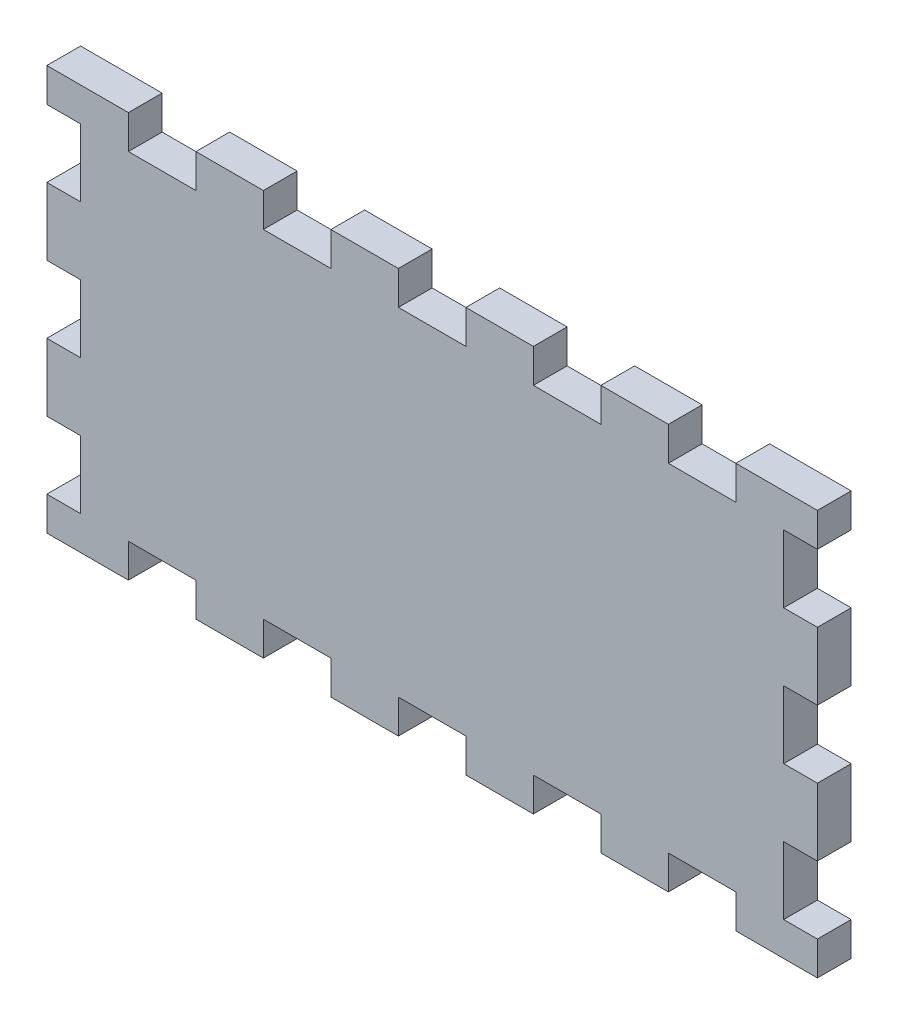
SolidWorks part; units mm, degrees
ref_plane "Front Plane" through (0, 0, 0) normal (0, 0, 1) x (1, 0, 0)
ref_plane "Top Plane" through (0, 0, 0) normal (0, 1, 0) x (1, 0, 0)
ref_plane "Right Plane" through (0, 0, 0) normal (1, 0, 0) x (0, 0, -1)
sketch "Sketch2" plane through (0, 0, 0) normal (0, 0, 1) x (1, 0, 0)
  line L0 (-68.5, 0) -> (-54, 0)
  line L1 (-54, 0) -> (-54, 6)
  line L2 (-54, 6) -> (-42, 6)
  line L3 (-42, 6) -> (-42, 0)
  line L4 (-42, 0) -> (-30, 0)
  line L5 (-30, 0) -> (-30, 6)
  line L6 (-30, 6) -> (-18, 6)
  line L7 (-18, 6) -> (-18, 0)
  line L8 (-18, 0) -> (-6, 0)
  line L9 (-6, 0) -> (-6, 6)
  line L10 (-6, 6) -> (6, 6)
  line L11 (6, 6) -> (6, 0)
  line L12 (6, 0) -> (18, 0)
  line L13 (18, 0) -> (18, 6)
  line L14 (18, 6) -> (30, 6)
  line L15 (30, 6) -> (30, 0)
  line L16 (30, 0) -> (42, 0)
  line L17 (42, 0) -> (42, 6)
  line L18 (42, 6) -> (54, 6)
  line L19 (54, 6) -> (54, 0)
  line L20 (54, 0) -> (68.5, 0)
  line L21 (68.5, 0) -> (68.5, 72)
  line L22 (-68.5, 0) -> (-68.5, 72)
  line L24 (54, 72) -> (68.5, 72)
  line L25 (54, 66) -> (54, 72)
  line L26 (42, 66) -> (54, 66)
  line L27 (42, 72) -> (42, 66)
  line L28 (30, 72) -> (42, 72)
  line L29 (30, 66) -> (30, 72)
  line L30 (18, 66) -> (30, 66)
  line L31 (18, 72) -> (18, 66)
  line L32 (6, 72) -> (18, 72)
  line L33 (6, 66) -> (6, 72)
  line L34 (-6, 66) -> (6, 66)
  line L35 (-6, 72) -> (-6, 66)
  line L36 (-18, 72) -> (-6, 72)
  line L37 (-18, 66) -> (-18, 72)
  line L38 (-30, 66) -> (-18, 66)
  line L39 (-30, 72) -> (-30, 66)
  line L40 (-42, 72) -> (-30, 72)
  line L41 (-42, 66) -> (-42, 72)
  line L42 (-54, 66) -> (-42, 66)
  line L43 (-54, 72) -> (-54, 66)
  line L44 (-68.5, 72) -> (-54, 72)
  line M1 (-54, 0) -> (-54, 6)
  line M2 (-54, 6) -> (-62.5, 6)
  line M3 (-62.5, 6) -> (-62.5, 0)
  dimension "D1" = 60
  dimension "D2" = 6
  dimension "D3" = 12
extrude "Boss-Extrude1" add sketch "Sketch2" along normal blind 6 contours L0 M3 M1 M2 | L44 L22 L0 L2 L3 L4 L5 L6 L7 L8 L9 L10 L11 L12 L13 L14 L15 L16 L17 L18 L19 L20 L21 L24 L25 L26 L27 L28 L29 L30 L31 L32 L33 L34 L35 L36 L37 L38 L39 L40 L41 L42 L43 M3 M2
sketch "Sketch3" plane through (0, 0, 6) normal (0, 0, 1) x (1, 0, 0)
  line L0 (-68.5, 0) -> (-68.5, 72) construction
  line L1 (-68.5, 6) -> (-62.5, 6)
  line L2 (-68.5, 6) -> (-68.5, 18)
  line L3 (-68.5, 18) -> (-62.5, 18)
  line L4 (-62.5, 6) -> (-62.5, 18)
  line L5 (62.5, 6) -> (62.5, 18)
  line L6 (62.5, 6) -> (68.5, 6)
  line L7 (68.5, 6) -> (68.5, 18)
  line L8 (62.5, 18) -> (68.5, 18)
  line L9 (62.5, 30) -> (62.5, 42)
  line L10 (62.5, 30) -> (68.5, 30)
  line L11 (68.5, 30) -> (68.5, 42)
  line L12 (62.5, 42) -> (68.5, 42)
  line L13 (62.5, 54) -> (62.5, 66)
  line L14 (62.5, 54) -> (68.5, 54)
  line L15 (68.5, 54) -> (68.5, 66)
  line L16 (62.5, 66) -> (68.5, 66)
  line L17 (-68.5, 30) -> (-68.5, 42)
  line L18 (-68.5, 30) -> (-62.5, 30)
  line L19 (-62.5, 30) -> (-62.5, 42)
  line L20 (-68.5, 42) -> (-62.5, 42)
  line L21 (-68.5, 54) -> (-68.5, 66)
  line L22 (-68.5, 54) -> (-62.5, 54)
  line L23 (-62.5, 54) -> (-62.5, 66)
  line L24 (-68.5, 66) -> (-62.5, 66)
  line L25 (68.5, 0) -> (68.5, 72) construction
  point P6 (-68.5, 36)
  line M26 (68.5, 0) -> (68.5, 72)
  line M48 (-68.5, 72) -> (-68.5, 0)
  dimension "D1" = 12
  dimension "D2" = 6
  dimension "D5" = 12
  dimension "D3" = 2
  dimension "D4" = 3
extrude "Cut-Extrude1" cut sketch "Sketch3" against normal blind 6 contours L24 L22 L23 M48 | L1 L4 L3 M48 | L12 L9 L10 M26 | L8 L5 L6 M26 | L17 L20 L19 L18 | L13 L16 L15 L14
